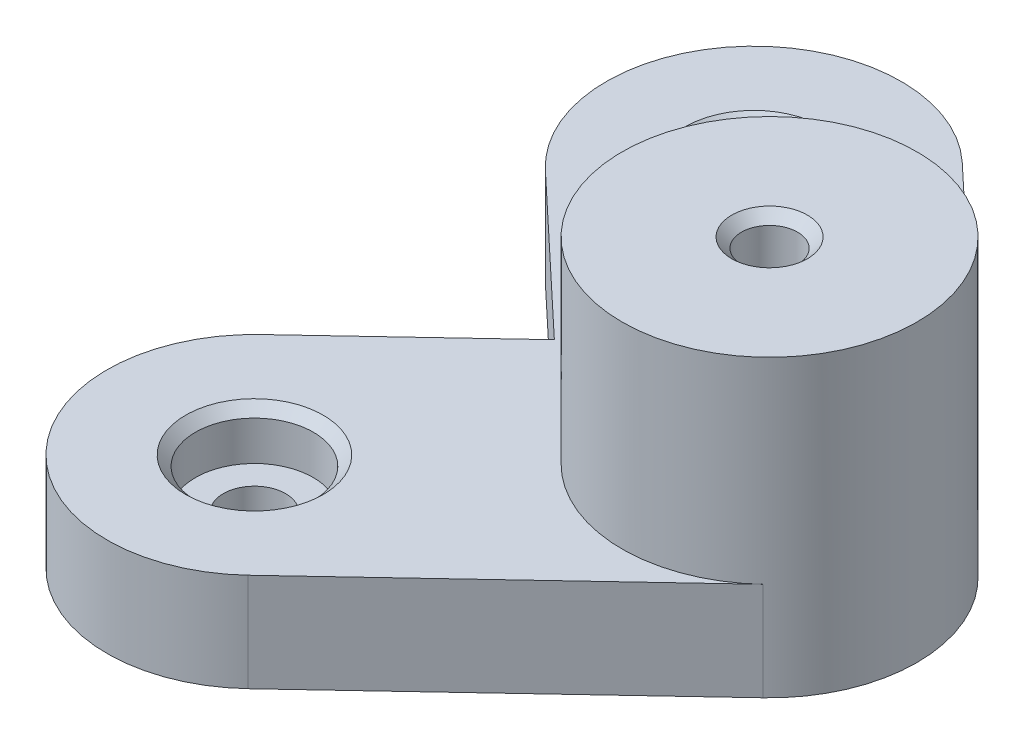
SolidWorks part; units mm, degrees
ref_plane "Front Plane" through (0, 0, 0) normal (0, 0, 1) x (1, 0, 0)
ref_plane "Top Plane" through (0, 0, 0) normal (0, 1, 0) x (1, 0, 0)
ref_plane "Right Plane" through (0, 0, 0) normal (1, 0, 0) x (0, 0, -1)
sketch "Sketch1" plane through (0, 0, 0) normal (0, 1, 0) x (1, 0, 0)
  circle A0 centre (0, 0) radius 100 construction
  circle A1 centre (-100, 0) radius 2.85
  circle A2 centre (-50, 86.6025) radius 2.85
  circle A3 centre (50, 86.6025) radius 2.85
  circle A4 centre (100, 0) radius 2.85
  circle A5 centre (50, -86.6025) radius 2.85
  circle A6 centre (-50, -86.6025) radius 2.85
  point P18 (0, 0)
  dimension "D1" = 200
  dimension "D2" = 5.7
  dimension "D3" = 6
sketch "Sketch3" plane through (0, 0, 0) normal (0, 1, 0) x (1, 0, 0)
  line L0 (-203.2, 152.4) -> (-203.2, -49.2102) construction
  line L1 (-203.2, 152.4) -> (37.0656, 152.4) construction
  circle A0 centre (-203.2, 152.4) radius 3.175
  circle A1 centre (-177.8, 152.4) radius 3.175
  circle A2 centre (-152.4, 152.4) radius 3.175
  circle A3 centre (-127, 152.4) radius 3.175
  circle A4 centre (-101.6, 152.4) radius 3.175
  circle A5 centre (-76.2, 152.4) radius 3.175
  circle A6 centre (-50.8, 152.4) radius 3.175
  circle A7 centre (-25.4, 152.4) radius 3.175
  circle A8 centre (0, 152.4) radius 3.175
  circle A9 centre (25.4, 152.4) radius 3.175
  circle A10 centre (50.8, 152.4) radius 3.175
  circle A11 centre (76.2, 152.4) radius 3.175
  circle A12 centre (101.6, 152.4) radius 3.175
  circle A13 centre (127, 152.4) radius 3.175
  circle A14 centre (152.4, 152.4) radius 3.175
  circle A15 centre (-177.8, 127) radius 3.175
  circle A16 centre (-152.4, 127) radius 3.175
  circle A17 centre (-127, 127) radius 3.175
  circle A18 centre (-101.6, 127) radius 3.175
  circle A19 centre (-76.2, 127) radius 3.175
  circle A20 centre (-50.8, 127) radius 3.175
  circle A21 centre (-25.4, 127) radius 3.175
  circle A22 centre (0, 127) radius 3.175
  circle A23 centre (25.4, 127) radius 3.175
  circle A24 centre (50.8, 127) radius 3.175
  circle A25 centre (76.2, 127) radius 3.175
  circle A26 centre (101.6, 127) radius 3.175
  circle A27 centre (127, 127) radius 3.175
  circle A28 centre (152.4, 127) radius 3.175
  circle A29 centre (-177.8, 101.6) radius 3.175
  circle A30 centre (-152.4, 101.6) radius 3.175
  circle A31 centre (-127, 101.6) radius 3.175
  circle A32 centre (-101.6, 101.6) radius 3.175
  circle A33 centre (-76.2, 101.6) radius 3.175
  circle A34 centre (-50.8, 101.6) radius 3.175
  circle A35 centre (-25.4, 101.6) radius 3.175
  circle A36 centre (0, 101.6) radius 3.175
  circle A37 centre (25.4, 101.6) radius 3.175
  circle A38 centre (50.8, 101.6) radius 3.175
  circle A39 centre (76.2, 101.6) radius 3.175
  circle A40 centre (101.6, 101.6) radius 3.175
  circle A41 centre (127, 101.6) radius 3.175
  circle A42 centre (152.4, 101.6) radius 3.175
  circle A43 centre (-177.8, 76.2) radius 3.175
  circle A44 centre (-152.4, 76.2) radius 3.175
  circle A45 centre (-127, 76.2) radius 3.175
  circle A46 centre (-101.6, 76.2) radius 3.175
  circle A47 centre (-76.2, 76.2) radius 3.175
  circle A48 centre (-50.8, 76.2) radius 3.175
  circle A49 centre (-25.4, 76.2) radius 3.175
  circle A50 centre (0, 76.2) radius 3.175
  circle A51 centre (25.4, 76.2) radius 3.175
  circle A52 centre (50.8, 76.2) radius 3.175
  circle A53 centre (76.2, 76.2) radius 3.175
  circle A54 centre (101.6, 76.2) radius 3.175
  circle A55 centre (127, 76.2) radius 3.175
  circle A56 centre (152.4, 76.2) radius 3.175
  circle A57 centre (-177.8, 50.8) radius 3.175
  circle A58 centre (-152.4, 50.8) radius 3.175
  circle A59 centre (-127, 50.8) radius 3.175
  circle A60 centre (-101.6, 50.8) radius 3.175
  circle A61 centre (-76.2, 50.8) radius 3.175
  circle A62 centre (-50.8, 50.8) radius 3.175
  circle A63 centre (-25.4, 50.8) radius 3.175
  circle A64 centre (0, 50.8) radius 3.175
  circle A65 centre (25.4, 50.8) radius 3.175
  circle A66 centre (50.8, 50.8) radius 3.175
  circle A67 centre (76.2, 50.8) radius 3.175
  circle A68 centre (101.6, 50.8) radius 3.175
  circle A69 centre (127, 50.8) radius 3.175
  circle A70 centre (152.4, 50.8) radius 3.175
  circle A71 centre (-177.8, 25.4) radius 3.175
  circle A72 centre (-152.4, 25.4) radius 3.175
  circle A73 centre (-127, 25.4) radius 3.175
  circle A74 centre (-101.6, 25.4) radius 3.175
  circle A75 centre (-76.2, 25.4) radius 3.175
  circle A76 centre (-50.8, 25.4) radius 3.175
  circle A77 centre (-25.4, 25.4) radius 3.175
  circle A78 centre (0, 25.4) radius 3.175
  circle A79 centre (25.4, 25.4) radius 3.175
  circle A80 centre (50.8, 25.4) radius 3.175
  circle A81 centre (76.2, 25.4) radius 3.175
  circle A82 centre (101.6, 25.4) radius 3.175
  circle A83 centre (127, 25.4) radius 3.175
  circle A84 centre (152.4, 25.4) radius 3.175
  circle A85 centre (-177.8, 0) radius 3.175
  circle A86 centre (-152.4, 0) radius 3.175
  circle A87 centre (-127, 0) radius 3.175
  circle A88 centre (-101.6, 0) radius 3.175
  circle A89 centre (-76.2, 0) radius 3.175
  circle A90 centre (-50.8, 0) radius 3.175
  circle A91 centre (-25.4, 0) radius 3.175
  circle A92 centre (0, 0) radius 3.175
  circle A93 centre (25.4, 0) radius 3.175
  circle A94 centre (50.8, 0) radius 3.175
  circle A95 centre (76.2, 0) radius 3.175
  circle A96 centre (101.6, 0) radius 3.175
  circle A97 centre (127, 0) radius 3.175
  circle A98 centre (152.4, 0) radius 3.175
  circle A99 centre (-177.8, -25.4) radius 3.175
  circle A100 centre (-152.4, -25.4) radius 3.175
  circle A101 centre (-127, -25.4) radius 3.175
  circle A102 centre (-101.6, -25.4) radius 3.175
  circle A103 centre (-76.2, -25.4) radius 3.175
  circle A104 centre (-50.8, -25.4) radius 3.175
  circle A105 centre (-25.4, -25.4) radius 3.175
  circle A106 centre (0, -25.4) radius 3.175
  circle A107 centre (25.4, -25.4) radius 3.175
  circle A108 centre (50.8, -25.4) radius 3.175
  circle A109 centre (76.2, -25.4) radius 3.175
  circle A110 centre (101.6, -25.4) radius 3.175
  circle A111 centre (127, -25.4) radius 3.175
  circle A112 centre (152.4, -25.4) radius 3.175
  circle A113 centre (-177.8, -50.8) radius 3.175
  circle A114 centre (-152.4, -50.8) radius 3.175
  circle A115 centre (-127, -50.8) radius 3.175
  circle A116 centre (-101.6, -50.8) radius 3.175
  circle A117 centre (-76.2, -50.8) radius 3.175
  circle A118 centre (-50.8, -50.8) radius 3.175
  circle A119 centre (-25.4, -50.8) radius 3.175
  circle A120 centre (0, -50.8) radius 3.175
  circle A121 centre (25.4, -50.8) radius 3.175
  circle A122 centre (50.8, -50.8) radius 3.175
  circle A123 centre (76.2, -50.8) radius 3.175
  circle A124 centre (101.6, -50.8) radius 3.175
  circle A125 centre (127, -50.8) radius 3.175
  circle A126 centre (152.4, -50.8) radius 3.175
  circle A127 centre (-177.8, -76.2) radius 3.175
  circle A128 centre (-152.4, -76.2) radius 3.175
  circle A129 centre (-127, -76.2) radius 3.175
  circle A130 centre (-101.6, -76.2) radius 3.175
  circle A131 centre (-76.2, -76.2) radius 3.175
  circle A132 centre (-50.8, -76.2) radius 3.175
  circle A133 centre (-25.4, -76.2) radius 3.175
  circle A134 centre (0, -76.2) radius 3.175
  circle A135 centre (25.4, -76.2) radius 3.175
  circle A136 centre (50.8, -76.2) radius 3.175
  circle A137 centre (76.2, -76.2) radius 3.175
  circle A138 centre (101.6, -76.2) radius 3.175
  circle A139 centre (127, -76.2) radius 3.175
  circle A140 centre (152.4, -76.2) radius 3.175
  circle A141 centre (-177.8, -101.6) radius 3.175
  circle A142 centre (-152.4, -101.6) radius 3.175
  circle A143 centre (-127, -101.6) radius 3.175
  circle A144 centre (-101.6, -101.6) radius 3.175
  circle A145 centre (-76.2, -101.6) radius 3.175
  circle A146 centre (-50.8, -101.6) radius 3.175
  circle A147 centre (-25.4, -101.6) radius 3.175
  circle A148 centre (0, -101.6) radius 3.175
  circle A149 centre (25.4, -101.6) radius 3.175
  circle A150 centre (50.8, -101.6) radius 3.175
  circle A151 centre (76.2, -101.6) radius 3.175
  circle A152 centre (101.6, -101.6) radius 3.175
  circle A153 centre (127, -101.6) radius 3.175
  circle A154 centre (152.4, -101.6) radius 3.175
  circle A155 centre (-177.8, -127) radius 3.175
  circle A156 centre (-152.4, -127) radius 3.175
  circle A157 centre (-127, -127) radius 3.175
  circle A158 centre (-101.6, -127) radius 3.175
  circle A159 centre (-76.2, -127) radius 3.175
  circle A160 centre (-50.8, -127) radius 3.175
  circle A161 centre (-25.4, -127) radius 3.175
  circle A162 centre (0, -127) radius 3.175
  circle A163 centre (25.4, -127) radius 3.175
  circle A164 centre (50.8, -127) radius 3.175
  circle A165 centre (76.2, -127) radius 3.175
  circle A166 centre (101.6, -127) radius 3.175
  circle A167 centre (127, -127) radius 3.175
  circle A168 centre (152.4, -127) radius 3.175
  circle A169 centre (-177.8, -152.4) radius 3.175
  circle A170 centre (-152.4, -152.4) radius 3.175
  circle A171 centre (-127, -152.4) radius 3.175
  circle A172 centre (-101.6, -152.4) radius 3.175
  circle A173 centre (-76.2, -152.4) radius 3.175
  circle A174 centre (-50.8, -152.4) radius 3.175
  circle A175 centre (-25.4, -152.4) radius 3.175
  circle A176 centre (0, -152.4) radius 3.175
  circle A177 centre (25.4, -152.4) radius 3.175
  circle A178 centre (50.8, -152.4) radius 3.175
  circle A179 centre (76.2, -152.4) radius 3.175
  circle A180 centre (101.6, -152.4) radius 3.175
  circle A181 centre (127, -152.4) radius 3.175
  circle A182 centre (152.4, -152.4) radius 3.175
  circle A183 centre (-177.8, -177.8) radius 3.175
  circle A184 centre (-152.4, -177.8) radius 3.175
  circle A185 centre (-127, -177.8) radius 3.175
  circle A186 centre (-101.6, -177.8) radius 3.175
  circle A187 centre (-76.2, -177.8) radius 3.175
  circle A188 centre (-50.8, -177.8) radius 3.175
  circle A189 centre (-25.4, -177.8) radius 3.175
  circle A190 centre (0, -177.8) radius 3.175
  circle A191 centre (25.4, -177.8) radius 3.175
  circle A192 centre (50.8, -177.8) radius 3.175
  circle A193 centre (76.2, -177.8) radius 3.175
  circle A194 centre (101.6, -177.8) radius 3.175
  circle A195 centre (127, -177.8) radius 3.175
  circle A196 centre (152.4, -177.8) radius 3.175
  circle A197 centre (-177.8, -203.2) radius 3.175
  circle A198 centre (-152.4, -203.2) radius 3.175
  circle A199 centre (-127, -203.2) radius 3.175
  circle A200 centre (-101.6, -203.2) radius 3.175
  circle A201 centre (-76.2, -203.2) radius 3.175
  circle A202 centre (-50.8, -203.2) radius 3.175
  circle A203 centre (-25.4, -203.2) radius 3.175
  circle A204 centre (0, -203.2) radius 3.175
  circle A205 centre (25.4, -203.2) radius 3.175
  circle A206 centre (50.8, -203.2) radius 3.175
  circle A207 centre (76.2, -203.2) radius 3.175
  circle A208 centre (101.6, -203.2) radius 3.175
  circle A209 centre (127, -203.2) radius 3.175
  circle A210 centre (152.4, -203.2) radius 3.175
  circle A211 centre (-203.2, 127) radius 3.175
  circle A212 centre (-203.2, 101.6) radius 3.175
  circle A213 centre (-203.2, 76.2) radius 3.175
  circle A214 centre (-203.2, 50.8) radius 3.175
  circle A215 centre (-203.2, 25.4) radius 3.175
  circle A216 centre (-203.2, 0) radius 3.175
  circle A217 centre (-203.2, -25.4) radius 3.175
  circle A218 centre (-203.2, -50.8) radius 3.175
  circle A219 centre (-203.2, -76.2) radius 3.175
  circle A220 centre (-203.2, -101.6) radius 3.175
  circle A221 centre (-203.2, -127) radius 3.175
  circle A222 centre (-203.2, -152.4) radius 3.175
  circle A223 centre (-203.2, -177.8) radius 3.175
  circle A224 centre (-203.2, -203.2) radius 3.175
  point P3 (-193.6728, 158.6667)
  point P6 (0, 0)
  dimension "D1" = 6.35
  dimension "D2" = 15
sketch "Sketch4" plane through (0, 0, 0) normal (0, 1, 0) x (1, 0, 0)
  line L0 (-100, 0) -> (-127, 25.4) construction
  line L2 (-89.7221, 10.9254) -> (-116.7221, 36.3254)
  line L3 (-100, 0) -> (-127, -25.4) construction
  line L4 (-89.7221, -10.9254) -> (-116.7221, -36.3254)
  line L6 (-121.8915, 0) -> (-137.2779, -14.4746)
  line L7 (-121.8915, 0) -> (-137.2779, 14.4746)
  arc A1 (-116.7221, 36.3254) -> (-137.2779, 14.4746) centre (-127, 25.4) ccw
  arc A3 (-137.2779, -14.4746) -> (-116.7221, -36.3254) centre (-127, -25.4) ccw
  arc A4 (-89.7221, -10.9254) -> (-89.7221, 10.9254) centre (-100, 0) ccw
  circle A5 centre (-127, 25.4) radius 3.175
  circle A6 centre (-127, -25.4) radius 3.175
  point P4 (-113.5, 12.7)
  point P9 (-113.5, -12.7)
  point P15 (0, 0)
  point P17 (0, 0)
  point P19 (0, 0)
  point P20 (0, 0)
  point P21 (0, 0)
  point P22 (0, 0)
  point P23 (0, 0)
  dimension "D1" = 6.35
  dimension "D2" = 6.35
extrude "Boss-Extrude1" add sketch "Sketch4" along normal blind 10
sketch "Sketch5" plane through (0, 10, 0) normal (0, 1, 0) x (1, 0, 0)
  circle A0 centre (-100, 0) radius 15
extrude "Boss-Extrude2" add sketch "Sketch5" along normal blind 20
sketch "Sketch6" plane through (0, 30, 0) normal (0, 1, 0) x (1, 0, 0)
  circle A0 centre (-100, 0) radius 2.85
  circle A1 centre (-100, 0) radius 2.85 construction
extrude "Cut-Extrude1" cut sketch "Sketch6" against normal blind 38
sketch "Sketch7" plane through (0, 10, 0) normal (0, 1, 0) x (1, 0, 0)
  circle A0 centre (-127, -25.4) radius 6
  dimension "D1" = 12
extrude "Cut-Extrude2" cut sketch "Sketch7" against normal blind 5
sketch "Sketch8" plane through (0, 10, 0) normal (0, 1, 0) x (1, 0, 0)
  circle A0 centre (-127, 25.4) radius 6
  dimension "D1" = 12
extrude "Cut-Extrude3" cut sketch "Sketch8" against normal blind 5
chamfer "Chamfer1" distance 1 angle 45 3 edges at (-100, 30, 2.85) (-127, 10, 31.4) (-127, 10, -19.4)
